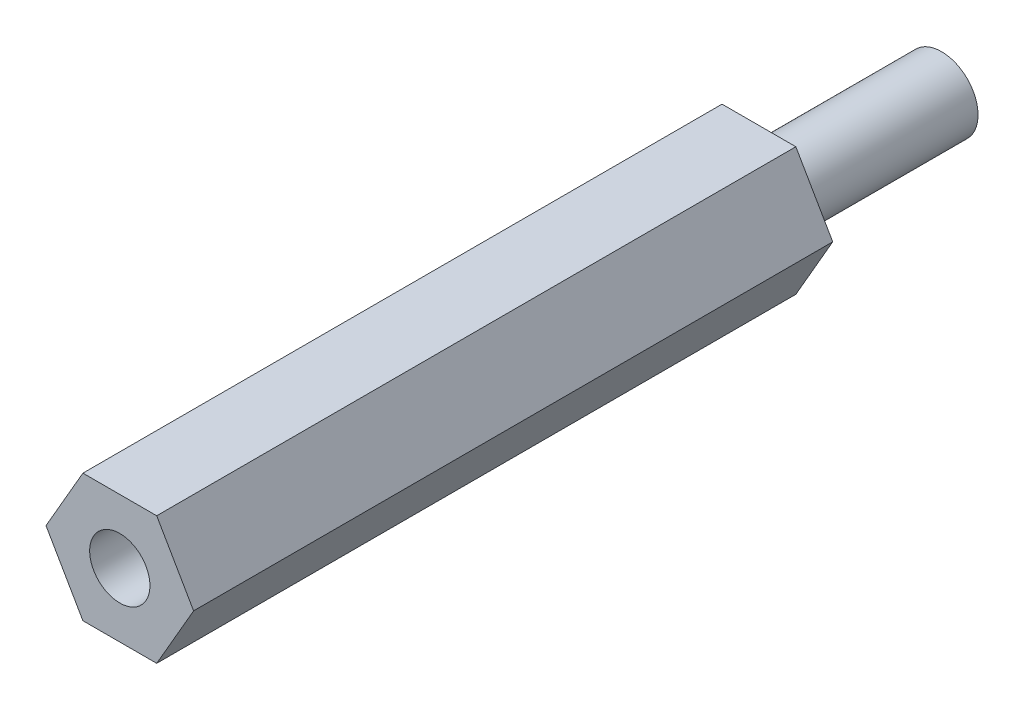
SolidWorks part; units mm, degrees
material "黃銅"
ref_plane "前基準面" through (0, 0, 0) normal (0, 0, 1) x (1, 0, 0)
ref_plane "上基準面" through (0, 0, 0) normal (0, 1, 0) x (1, 0, 0)
ref_plane "右基準面" through (0, 0, 0) normal (1, 0, 0) x (0, 0, -1)
sketch "草圖1" plane through (0, 0, 0) normal (0, 0, 1) x (1, 0, 0)
  line L1 (-2.0207, 3.5) -> (-4.0415, 0)
  line L2 (-4.0415, 0) -> (-2.0207, -3.5)
  line L3 (-2.0207, -3.5) -> (2.0207, -3.5)
  line L4 (2.0207, -3.5) -> (4.0415, 0)
  line L5 (4.0415, 0) -> (2.0207, 3.5)
  line L6 (2.0207, 3.5) -> (-2.0207, 3.5)
  circle A0 centre (0, 0) radius 3.5 construction
  dimension "D1" = 7
extrude "填料-伸長1" add sketch "草圖1" along normal blind 35
sketch "草圖4" plane through (0, 0, 0) normal (0, 0, -1) x (-1, 0, 0)
  circle A0 centre (0, 0) radius 2
  dimension "D1" = 4
extrude "填料-伸長2" add sketch "草圖4" along normal blind 10
hole_wizard "M4x0.7 螺紋孔1" positions "草圖2" profile "草圖3" tap size "M4x0.7" standard "Ansi Metric"
sketch "草圖2" plane through (0, 0, 35) normal (0, 0, 1) x (1, 0, 0)
  point P0 (0, 0)
sketch "草圖3" plane through (0, 0, 35) normal (1, 0, 0) x (0, -1, 0)
  line L0 (0, 0) -> (0, 11.0914)
  line L1 (0, 11.0914) -> (1.65, 10.1)
  line L2 (1.65, 10.1) -> (1.65, 0)
  line L5 (1.65, 0) -> (0, 0)
  line L10 (0, 11.0914) -> (-1.65, 10.1) construction
  line L11 (0, -6.35) -> (0, 107.95) construction
  dimension "螺孔鑽直徑" = 3.3
  dimension "螺孔鑽深度" = 10.1
  dimension "導頭角度" = 118
